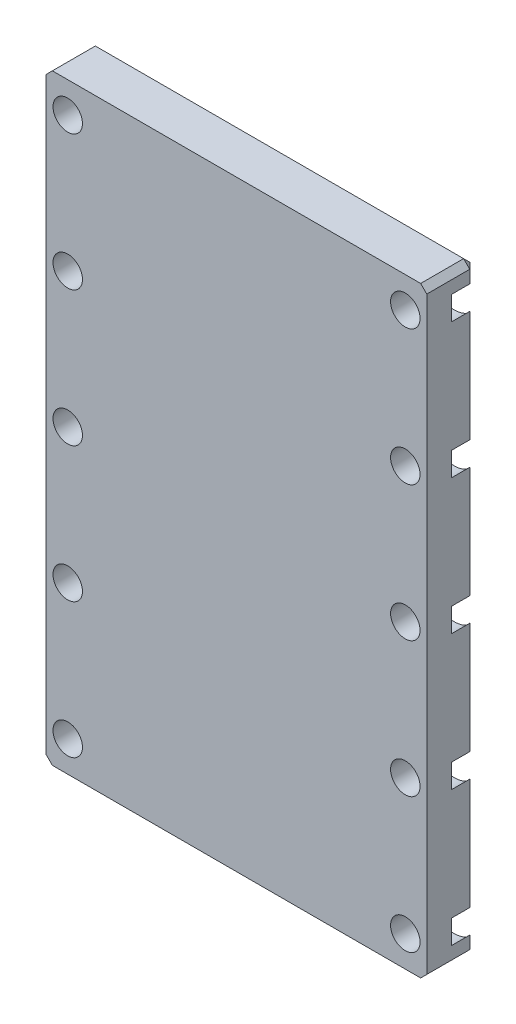
SolidWorks part; units mm, degrees
material "ABS"
ref_plane "正面" through (0, 0, 0) normal (0, 0, 1) x (1, 0, 0)
ref_plane "平面" through (0, 0, 0) normal (0, 1, 0) x (1, 0, 0)
ref_plane "右側面" through (0, 0, 0) normal (1, 0, 0) x (0, 0, -1)
sketch "ｽｹｯﾁ1" plane through (0, 0, 0) normal (0, 0, 1) x (1, 0, 0)
  line L1 (-31, 49) -> (31, 49)
  line L2 (-31, 49) -> (-31, -49)
  line L3 (-31, -49) -> (31, -49)
  line L4 (31, 49) -> (31, -49)
  line L5 (-31, 49) -> (31, -49) construction
  line L6 (-31, -49) -> (31, 49) construction
  point P0 (0, 0)
  dimension "D1" = 98
  dimension "D2" = 62
extrude "ﾎﾞｽ - 押し出し1" add sketch "ｽｹｯﾁ1" along normal blind 8
sketch "ｽｹｯﾁ2" plane through (0, 0, 8) normal (0, 0, 1) x (1, 0, 0)
  line L0 (0, 49) -> (0, -49) construction
  line L1 (31, 49) -> (-31, 49) construction
  line L2 (-31, -49) -> (31, -49) construction
  line L3 (-27.5, 49) -> (-27.5, -49) construction
  line L4 (-31, 0) -> (31, 0) construction
  line L5 (-31, 49) -> (-31, -49) construction
  line L6 (31, -49) -> (31, 49) construction
  dimension "D1" = 27.5
chamfer "面取り1" distance 1 angle 45 8 edges at (0, 49, 0) (31, 49, 4) (31, 0, 0) (31, -49, 4) (0, -49, 0) (-31, -49, 4) (-31, 0, 0) (-31, 49, 4)
hole_wizard "M4 穴付きねじ用座ぐり穴1" positions "ｽｹｯﾁ4" profile "ｽｹｯﾁ5" counterbore size "M4" standard "JIS" end condition through all
sketch "ｽｹｯﾁ4" plane through (0, 0, 0) normal (0, 0, 1) x (1, 0, 0)
  line L0 (-27.5, 49) -> (-27.5, -49) construction
  line L1 (30, 49) -> (-30, 49) construction
  line L2 (-31, 22) -> (31, 22) construction
  line L3 (-31, 48) -> (-31, -48) construction
  line L4 (31, -48) -> (31, 48) construction
  point P0 (-27.5, 44)
  point P7 (-27.5, 22)
  point P9 (-27.5, 0)
  dimension "D1" = 5
sketch "ｽｹｯﾁ5" plane through (-27.5, 44, 0) normal (1, 0, 0) x (0, 1, 0)
  line L0 (0, 0) -> (0, 8)
  line L1 (0, 8) -> (2.4, 8)
  line L3 (2.4, 8) -> (2.4, 4)
  line L4 (2.4, 4) -> (4, 4)
  line L5 (4, 4) -> (4, 0)
  line L7 (4, 0) -> (0, 0)
  line L11 (0, -6.35) -> (0, 107.95) construction
  dimension "通し穴の直径" = 4.8
  dimension "通し穴の深さ" = 8
  dimension "座ぐり穴の直径" = 8
  dimension "座ぐり穴の深さ" = 4
sketch "ｽｹｯﾁ6" plane through (0, 0, 0) normal (0, 0, -1) x (-1, 0, 0)
  line L0 (27.5, 18.7668) -> (30.3, 20.3834)
  line L1 (27.5, 40.7668) -> (30.3, 42.3834)
  line L2 (30.3, 42.3834) -> (30.3, 45.6166)
  line L3 (30.3, 45.6166) -> (27.5, 47.2332)
  line L4 (27.5, 47.2332) -> (24.7, 45.6166)
  line L5 (24.7, 45.6166) -> (24.7, 42.3834)
  line L6 (24.7, 42.3834) -> (27.5, 40.7668)
  line L7 (30.3, 20.3834) -> (30.3, 23.6166)
  line L8 (30.3, 23.6166) -> (27.5, 25.2332)
  line L9 (27.5, 25.2332) -> (24.7, 23.6166)
  line L10 (24.7, 23.6166) -> (24.7, 20.3834)
  line L11 (24.7, 20.3834) -> (27.5, 18.7668)
  line L12 (27.5, -3.2332) -> (30.3, -1.6166)
  line L13 (30.3, -1.6166) -> (30.3, 1.6166)
  line L14 (30.3, 1.6166) -> (27.5, 3.2332)
  line L15 (27.5, 3.2332) -> (24.7, 1.6166)
  line L16 (24.7, 1.6166) -> (24.7, -1.6166)
  line L17 (24.7, -1.6166) -> (27.5, -3.2332)
  circle A0 centre (27.5, 44) radius 2.8 construction
  circle A1 centre (27.5, 22) radius 2.8 construction
  circle A2 centre (27.5, 0) radius 2.8 construction
  circle A3 centre (27.5, 22) radius 4 construction
  dimension "D1" = 5.6
  dimension "D2" = 3
extrude "ｶｯﾄ - 押し出し1" [suppressed] cut sketch "ｽｹｯﾁ6" against normal blind 2.5
sketch "ｽｹｯﾁ7" [suppressed] plane through (0, 0, 0) normal (0, 0, -1) x (-1, 0, 0)
  circle A0 centre (27.5, 47.2332) radius 0.5
  dimension "D1" = 1
extrude "ｶｯﾄ - 押し出し2" [suppressed] cut sketch "ｽｹｯﾁ7" against normal blind 2.5
pattern_circular "円形ﾊﾟﾀｰﾝ1" [suppressed] count 6 over 360
pattern_linear "直線ﾊﾟﾀｰﾝ1" [suppressed] count 3 spacing 22
mirror "ﾐﾗｰ1" about plane through (0, 0, 0) normal (0, 1, 0) of "M4 穴付きねじ用座ぐり穴1", "ｶｯﾄ - 押し出し1", "ｶｯﾄ - 押し出し2", "直線ﾊﾟﾀｰﾝ1", "円形ﾊﾟﾀｰﾝ1"
mirror "ﾐﾗｰ2" about plane through (0, 0, 0) normal (1, 0, 0) of "ﾐﾗｰ1", "M4 穴付きねじ用座ぐり穴1"
